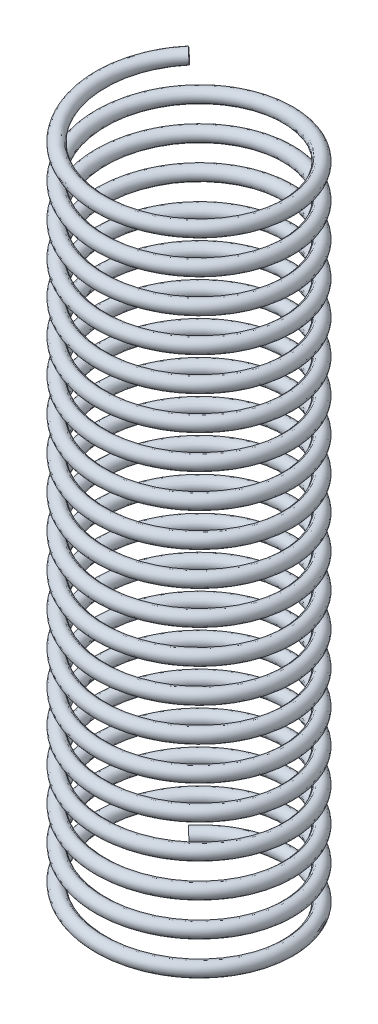
SolidWorks part; units mm, degrees
ref_plane "Front Plane" through (0, 0, 0) normal (0, 0, 1) x (1, 0, 0)
ref_plane "Top Plane" through (0, 0, 0) normal (0, 1, 0) x (1, 0, 0)
ref_plane "Right Plane" through (0, 0, 0) normal (1, 0, 0) x (0, 0, -1)
sketch "Sketch1" plane through (0, 0, 0) normal (0, 1, 0) x (1, 0, 0)
  circle A0 centre (0, 0) radius 13.9
  dimension "D1" = 27.8
curve "Helix/Spiral1" pitch 5 height 100 turns 20
sweep "Sweep1" add path "Helix/Spiral1" circular profile diameter 2 parameters "D3"=2
